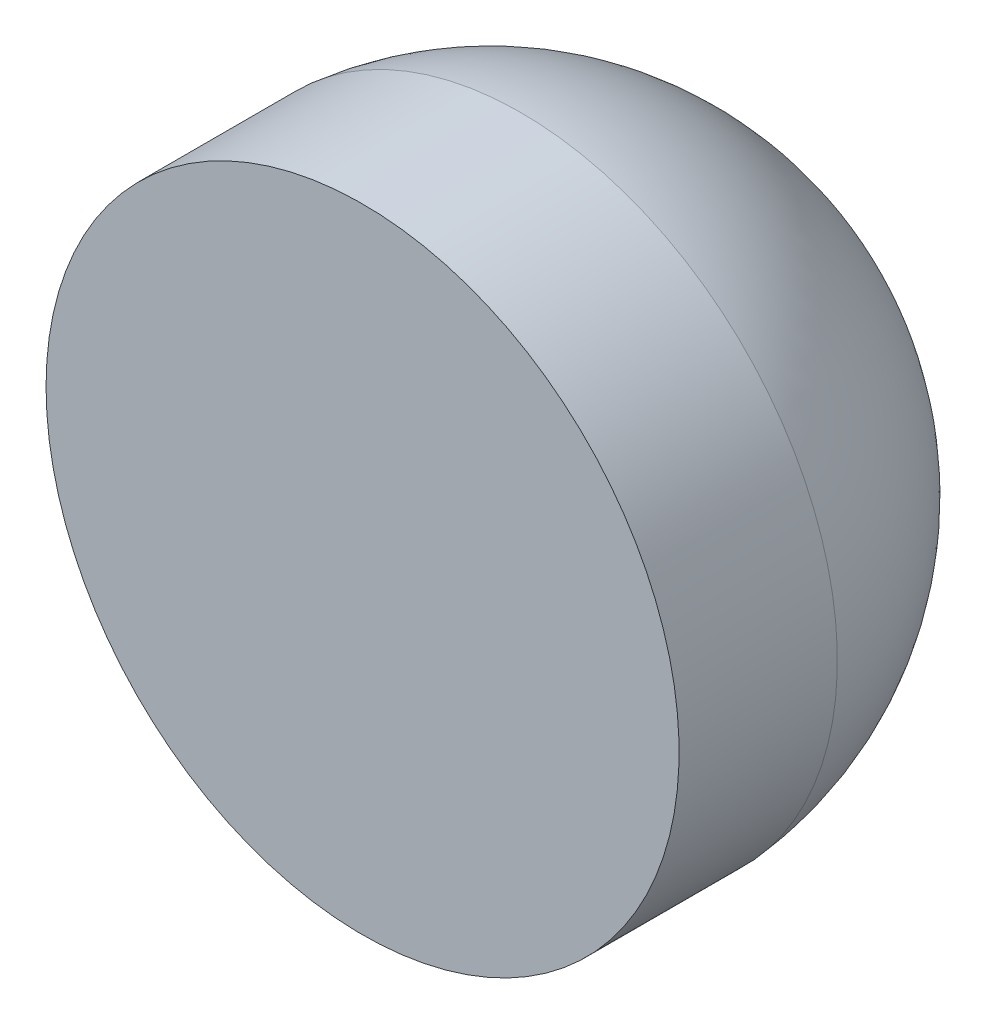
SolidWorks part; units mm, degrees
ref_plane "Front Plane" through (0, 0, 0) normal (0, 0, 1) x (1, 0, 0)
ref_plane "Top Plane" through (0, 0, 0) normal (0, 1, 0) x (1, 0, 0)
ref_plane "Right Plane" through (0, 0, 0) normal (1, 0, 0) x (0, 0, -1)
sketch "Sketch4" plane through (0, 0, 0) normal (0, 1, 0) x (1, 0, 0)
  line L0 (0, 5.9) -> (2.5, 5.9)
  line L1 (2.5, 5.9) -> (2.5, 7.9)
  line L2 (0, 5.9) -> (0, 0)
  line L3 (0, 0) -> (6, 0)
  line L4 (6, 0) -> (6, 3)
  arc A0 (2.5, 7.9) -> (6, 3) centre (0.0268, 2.4334) cw
  dimension "D1" = 6
  dimension "D2" = 3
  dimension "D3" = 5.9
  dimension "D4" = 2
  dimension "D5" = 2.5
  dimension "D6" = 6
revolve "Revolve1" add sketch "Sketch4" angle 360 about L2
